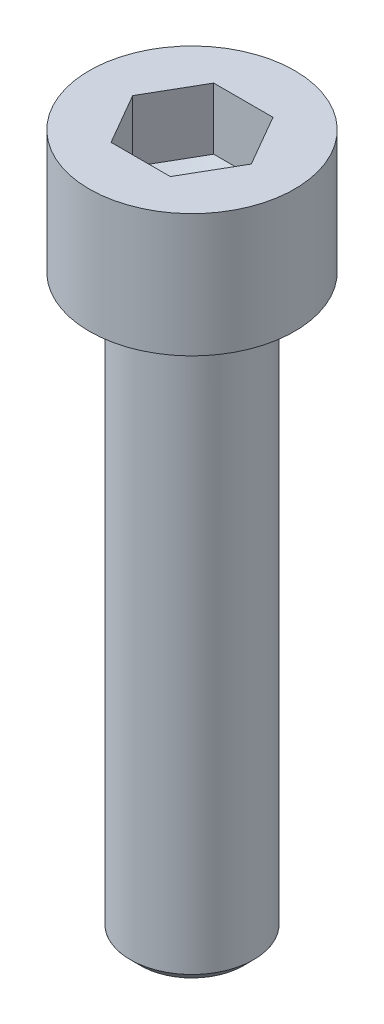
SolidWorks part; units mm, degrees
ref_plane "Front Plane" through (0, 0, 0) normal (0, 0, 1) x (1, 0, 0)
ref_plane "Top Plane" through (0, 0, 0) normal (0, 1, 0) x (1, 0, 0)
ref_plane "Right Plane" through (0, 0, 0) normal (1, 0, 0) x (0, 0, -1)
sketch "Sketch1" plane through (0, 0, 0) normal (0, 1, 0) x (1, 0, 0)
  circle A0 centre (0, 0) radius 5
extrude "Boss-Extrude1" add sketch "Sketch1" along normal blind 6
sketch "Sketch2" plane through (0, 6, 0) normal (0, 1, 0) x (1, 0, 0)
  line L1 (2.8868, 0) -> (1.4434, 2.5)
  line L2 (1.4434, 2.5) -> (-1.4434, 2.5)
  line L3 (-1.4434, 2.5) -> (-2.8868, 0)
  line L4 (-2.8868, 0) -> (-1.4434, -2.5)
  line L5 (-1.4434, -2.5) -> (1.4434, -2.5)
  line L6 (1.4434, -2.5) -> (2.8868, 0)
extrude "Cut-Extrude1" cut sketch "Sketch2" against normal blind 3
sketch "Sketch3" plane through (0, 3, 0) normal (0, 1, 0) x (1, 0, 0)
  circle A0 centre (0, 0) radius 2.8868
extrude "Cut-Extrude5" cut sketch "Sketch3" against normal blind 1 draft 75
sketch "Sketch4" plane through (0, 0, 0) normal (0, -1, 0) x (1, 0, 0)
  circle A0 centre (0, 0) radius 3
extrude "Boss-Extrude2" add sketch "Sketch4" along normal blind 27.5
sketch "Sketch5" plane through (0, -27.5, 0) normal (0, -1, 0) x (1, 0, 0)
  circle A0 centre (0, 0) radius 3
extrude "Boss-Extrude3" add sketch "Sketch5" along normal blind 0.5 draft 45 separate body
